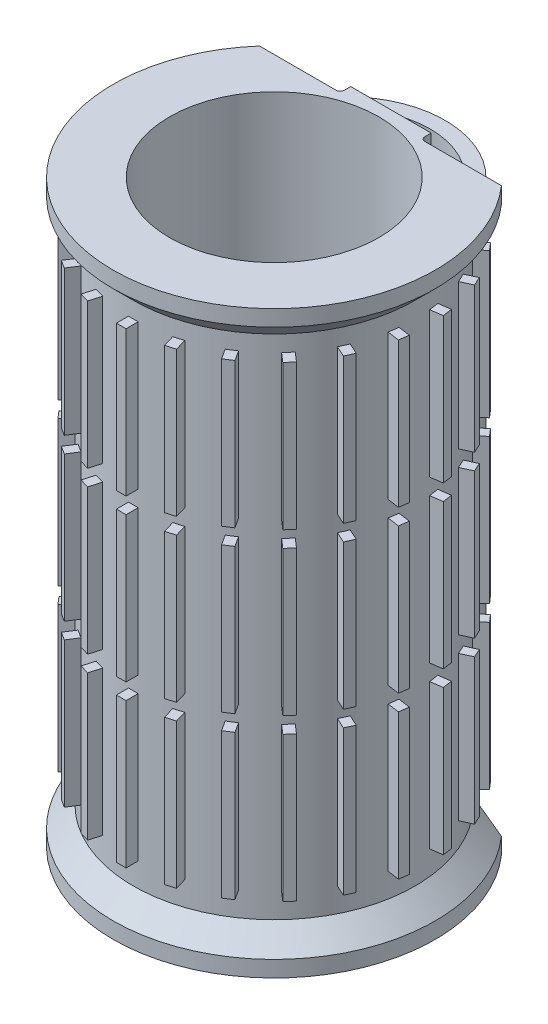
SolidWorks part; units mm, degrees
ref_plane "前视基准面" through (0, 0, 0) normal (0, 0, 1) x (1, 0, 0)
ref_plane "上视基准面" through (0, 0, 0) normal (0, 1, 0) x (1, 0, 0)
ref_plane "右视基准面" through (0, 0, 0) normal (1, 0, 0) x (0, 0, -1)
sketch "草图1" plane through (0, 0, 0) normal (0, 0, 1) x (1, 0, 0)
  line L0 (0, 0) -> (0, 90.6064) construction
  line L1 (0, 0) -> (20, 0)
  line L2 (20, 0) -> (20, 2)
  line L3 (20, 2) -> (17.5, 4.5)
  line L4 (17.5, 4.5) -> (17.5, 67.5)
  line L5 (17.5, 67.5) -> (20, 70)
  line L6 (20, 70) -> (20, 72)
  line L7 (20, 72) -> (0, 72)
  line L8 (0, 72) -> (0, 0)
  line L9 (13, 0) -> (13, 72)
  line L10 (0, 36) -> (20.3442, 36) construction
  dimension "D1" = 2
  dimension "D2" = 20
  dimension "D3" = 13
  dimension "D4" = 17.5
  dimension "D5" = 63
revolve "旋转1" add sketch "草图1" angle 360 about L0
ref_plane "基准面1" through (0, 0, 19) normal (0, 0, 1) x (1, 0, 0)
sketch "草图2" plane through (0, 0, 19) normal (0, 0, 1) x (1, 0, 0)
  line L0 (0, 67.5) -> (0, 4.5) construction
  line L1 (17.5, 67.5) -> (-17.5, 67.5) construction
  line L2 (17.5, 4.5) -> (-17.5, 4.5) construction
  line L3 (0.6, 45.5) -> (0.6, 27.5)
  line L4 (-0.6, 65.5) -> (0.6, 65.5)
  line L5 (-0.6, 65.5) -> (-0.6, 47.5)
  line L6 (-0.6, 47.5) -> (0.6, 47.5)
  line L7 (0.6, 65.5) -> (0.6, 47.5)
  line L8 (-0.6, 65.5) -> (0.6, 47.5) construction
  line L9 (-0.6, 47.5) -> (0.6, 65.5) construction
  line L10 (-0.6, 45.5) -> (-0.6, 27.5)
  line L11 (-0.6, 27.5) -> (0.6, 27.5)
  line L12 (-0.6, 45.5) -> (0.6, 45.5)
  line L13 (0.6, 25.5) -> (0.6, 7.5)
  line L14 (-0.6, 25.5) -> (-0.6, 7.5)
  line L15 (-0.6, 7.5) -> (0.6, 7.5)
  line L16 (-0.6, 25.5) -> (0.6, 25.5)
  point P6 (0, 56.5)
  dimension "D1" = 2
  dimension "D2" = 18
  dimension "D3" = 1.2
  dimension "D4" = 3
extrude "凸台-拉伸1" add sketch "草图2" against normal up to surface (1.5103 mm away)
pattern_circular "阵列(圆周)1" count 22 over 360 about axis through (0, 0, 0) along (0, 1, 0) of "凸台-拉伸1"
sketch "草图3" plane through (0, 72, 0) normal (0, 1, 0) x (1, 0, 0)
  line L0 (-15.0253, 13.2) -> (15.0253, 13.2)
  circle A0 centre (0, 0) radius 13 construction
  circle A1 centre (0, 0) radius 20 construction
  circle A2 centre (0, 0) radius 13
  circle A3 centre (0, 0) radius 20
  circle M2 centre (0, 0) radius 20
  dimension "D1" = 13.2
extrude "切除-拉伸1" cut sketch "草图3" against normal through all contours L0 M2
sketch "草图4" plane through (0, 72, 0) normal (0, 1, 0) x (1, 0, 0)
  line L0 (-5, 13.2) -> (-5, 14.5)
  line L1 (-15.0253, 13.2) -> (15.0253, 13.2) construction
  line L2 (-5, 14.5) -> (5, 14.5)
  line L3 (5, 14.5) -> (5, 13.2)
  line L4 (5, 13.2) -> (-5, 13.2)
  line L5 (0, 13) -> (0, 16.2163) construction
  circle A0 centre (0, 0) radius 13 construction
  dimension "D1" = 14.5
  dimension "D2" = 10
extrude "凸台-拉伸2" add sketch "草图4" against normal up to surface (72 mm away) up to face at (0, 0, 3.4)
sketch "草图5" plane through (0, 0, -13.2) normal (0, 0, -1) x (-1, 0, 0)
  line L1 (11.4896, 67.5) -> (9.4896, 67.5)
  line L2 (11.4896, 67.5) -> (11.4896, 4.5)
  line L3 (11.4896, 4.5) -> (9.4896, 4.5)
  line L4 (9.4896, 67.5) -> (9.4896, 4.5)
  dimension "D1" = 2
ref_plane "基准面2" through (0, 30, 0) normal (0, -1, 0) x (-1, 0, 0)
sketch "草图7" plane through (0, 30, 0) normal (0, -1, 0) x (-1, 0, 0)
  line L4 (11.4896, 13.2) -> (9.4896, 13.2) construction
  line L5 (0, 0) -> (0, 16.8493) construction
  arc A0 (10.4896, 13.2) -> (-11.2266, 10.2788) centre (0, 9) ccw
  dimension "D1" = 9
sweep "扫描1" add profiles "草图5" path "草图7"
fillet "圆角1" radius 0.5 2 edges at (5, 36, -13.2) (-5, 36, -13.2)
